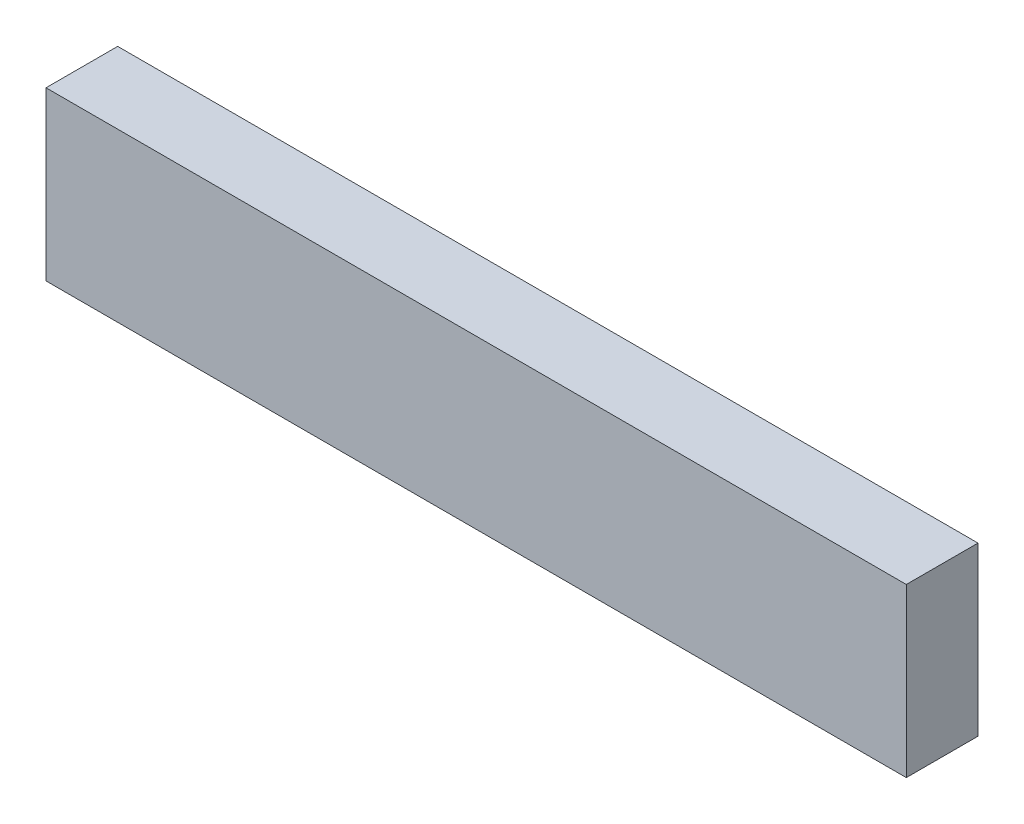
SolidWorks part; units mm, degrees
ref_plane "Front Plane" through (0, 0, 0) normal (0, 0, 1) x (1, 0, 0)
ref_plane "Top Plane" through (0, 0, 0) normal (0, 1, 0) x (1, 0, 0)
ref_plane "Right Plane" through (0, 0, 0) normal (1, 0, 0) x (0, 0, -1)
sketch "Sketch1" plane through (0, 0, 0) normal (0, 0, 1) x (1, 0, 0)
  line L1 (-228.6, 44.45) -> (228.6, 44.45)
  line L2 (-228.6, 44.45) -> (-228.6, -44.45)
  line L3 (-228.6, -44.45) -> (228.6, -44.45)
  line L4 (228.6, 44.45) -> (228.6, -44.45)
  line L5 (-228.6, 44.45) -> (228.6, -44.45) construction
  line L6 (-228.6, -44.45) -> (228.6, 44.45) construction
  point P0 (0, 0)
  dimension "D1" = 457.2
  dimension "D2" = 88.9
extrude "Boss-Extrude1" add sketch "Sketch1" along normal blind 38.1
